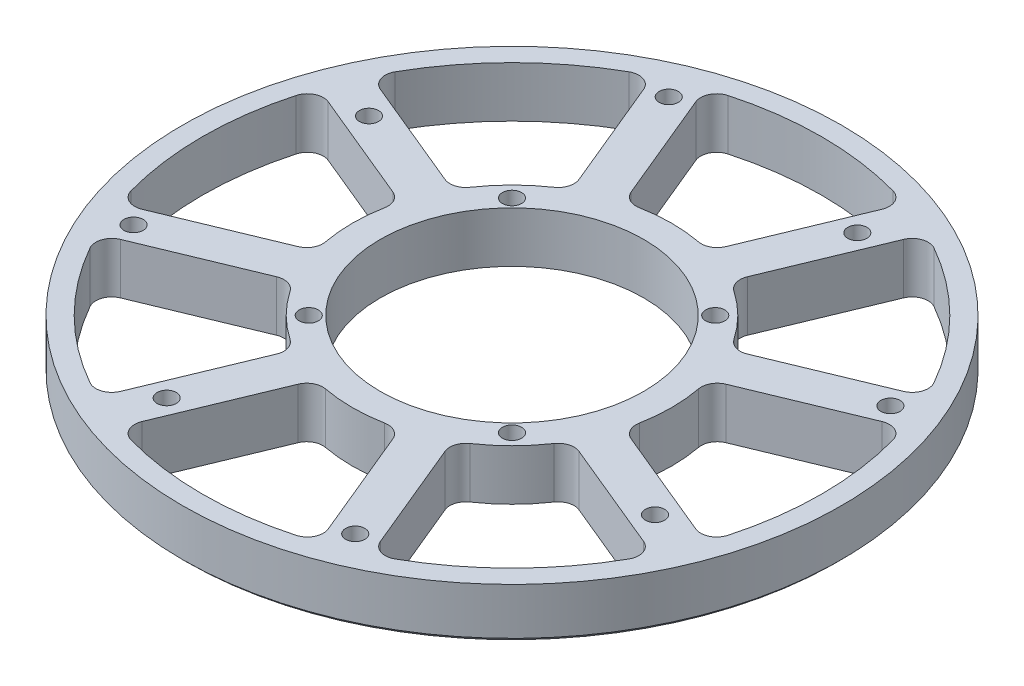
SolidWorks part; units mm, degrees
material "6061-T6 (SS)"
ref_plane "Front Plane" through (0, 0, 0) normal (0, 0, 1) x (1, 0, 0)
ref_plane "Top Plane" through (0, 0, 0) normal (0, 1, 0) x (1, 0, 0)
ref_plane "Right Plane" through (0, 0, 0) normal (1, 0, 0) x (0, 0, -1)
sketch "Sketch2" plane through (0, 0, 0) normal (1, 0, 0) x (0, 0, -1)
  line L0 (0, 0) -> (-82.55, 0)
  line L1 (-82.55, 0) -> (-82.55, 12.7)
  line L2 (-82.55, 12.7) -> (0, 12.7)
  line L5 (0, 12.7) -> (0, 0)
  dimension "D1" = 82.55
  dimension "D2" = 12.7
ref_axis "Axis1" through (0, -0.635, 0) along (0, 1, 0)
revolve "Revolve1" add sketch "Sketch2" angle 360 about axis through (0, -0.635, 0) along (0, 1, 0)
hole_wizard "#12 (0.189) Diameter Hole1" positions "Sketch6" profile "Sketch7" hole size "#12" standard "ANSI Inch" end condition through all
sketch "Sketch6" plane through (0, 12.7, 0) normal (0, 1, 0) x (1, 0, 0)
  line L0 (0, 0) -> (-53.438, 129.0108) construction
  line L2 (0, 0) -> (0, 109.0908) construction
  line L3 (0, 0) -> (-76.2663, 31.5905) construction
  line L4 (0, 0) -> (-68.4315, 68.4315) construction
  circle A0 centre (0, 0) radius 82.55 construction
  point P0 (-27.7637, 67.0275)
  point P18 (-61.1608, 25.3336)
  point P27 (-25.4558, 25.4558)
  dimension "D1" = 22.5
  dimension "D2" = 72.55
  dimension "D3" = 45
  dimension "D4" = 66.2
  dimension "D6" = 22.5
  dimension "D5" = 36
sketch "Sketch7" plane through (-27.7637, 12.7, -67.0275) normal (1, 0, 0) x (0, 0, 1)
  line L0 (0, 0) -> (0, 12.7)
  line L1 (0, 12.7) -> (2.4003, 12.7)
  line L2 (2.4003, 12.7) -> (2.4003, 0)
  line L5 (2.4003, 0) -> (0, 0)
  line L11 (0, -6.35) -> (0, 107.95) construction
  dimension "Thru Hole Dia." = 4.8006
  dimension "Thru Hole Depth" = 12.7
pattern_circular "CirPattern3" count 4 over 360 about axis through (0, 0, 0) along (0, 1, 0) of "#12 (0.189) Diameter Hole1"
sketch "Sketch8" plane through (0, 12.7, 0) normal (0, 1, 0) x (1, 0, 0)
  line L4 (0, 0) -> (0, 93.9995) construction
  line L5 (0, 0) -> (113.8372, 0) construction
  line L6 (-10.5679, 38.5787) -> (-24.996, 73.4112)
  line L7 (10.5679, 38.5787) -> (24.996, 73.4112)
  line L8 (0, 0) -> (-27.7637, 67.0275) construction
  arc A0 (-10.5679, 38.5787) -> (10.5679, 38.5787) centre (0, 0) cw
  arc A1 (-24.996, 73.4112) -> (24.996, 73.4112) centre (0, 0) cw
  circle A2 centre (0, 0) radius 82.55 construction
  dimension "D1" = 40
  dimension "D2" = 5
  dimension "D3" = 5
extrude "Cut-Extrude1" cut sketch "Sketch8" against normal through all
fillet "Fillet1" radius 4 4 edges at (10.5679, 6.35, -38.5787) (24.996, 6.35, -73.4112) (-10.5679, 6.35, -38.5787) (-24.996, 6.35, -73.4112)
pattern_circular "CirPattern4" count 8 over 360 about axis through (0, 0, 0) along (0, 1, 0) of "Cut-Extrude1", "Fillet1"
chamfer "Chamfer2" distance 1 angle 45 1 edges at (0, 0, -82.55)
sketch "Sketch9" plane through (0, 12.7, 0) normal (0, 1, 0) x (1, 0, 0)
  circle A0 centre (0, 0) radius 33
  dimension "D1" = 66
extrude "Cut-Extrude2" cut sketch "Sketch9" against normal through all
equation "\"TubeDiameter\"= 6.500in"
equation "\"D1@Sketch2\"=\"TubeDiameter\"/2"
equation "\"D2@Sketch6\"=\"TubeDiameter\"/2-10mm"
